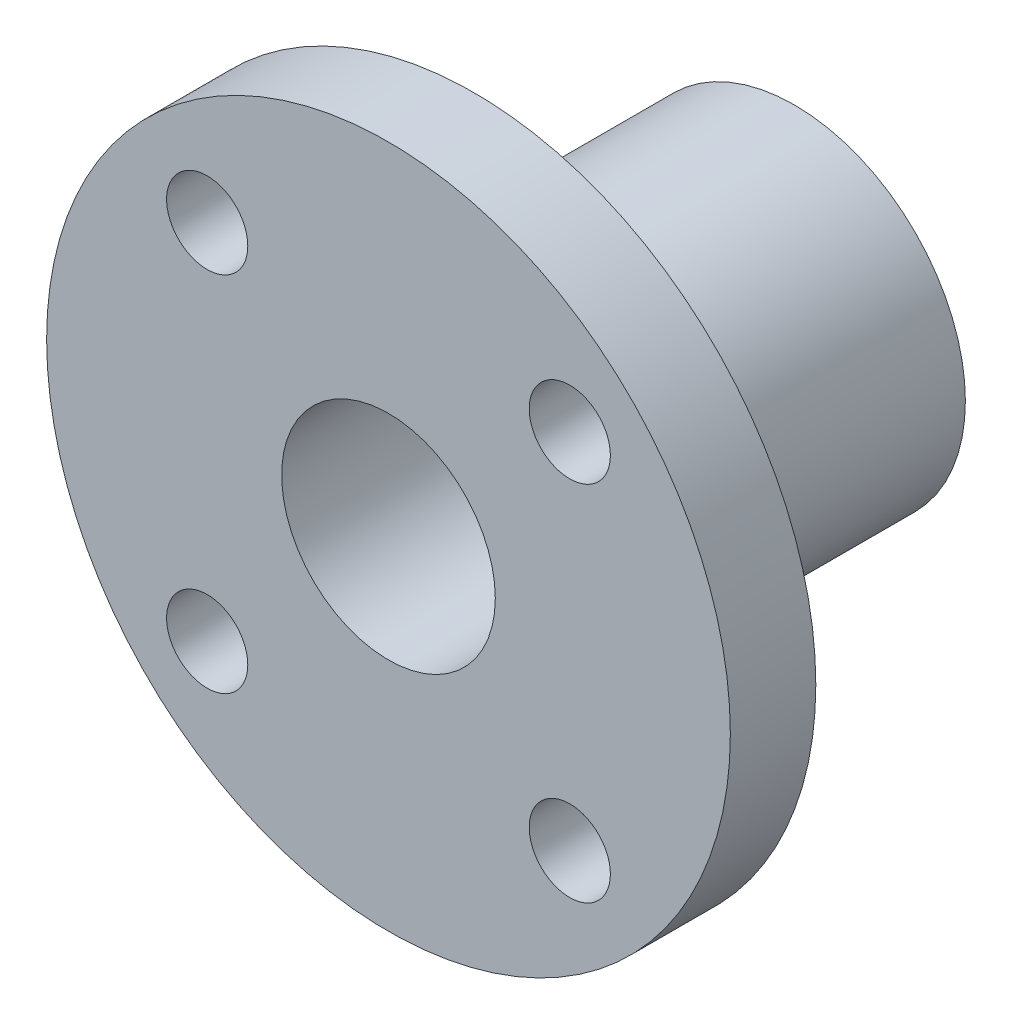
SolidWorks part; units mm, degrees
ref_plane "前视基准面" through (0, 0, 0) normal (0, 0, 1) x (1, 0, 0)
ref_plane "上视基准面" through (0, 0, 0) normal (0, 1, 0) x (1, 0, 0)
ref_plane "右视基准面" through (0, 0, 0) normal (1, 0, 0) x (0, 0, -1)
sketch "Sketch1" plane through (0, 0, 0) normal (0, 0, 1) x (1, 0, 0)
  circle A0 centre (0, 0) radius 8
  circle A1 centre (0, 0) radius 5
  dimension "D1" = 16
  dimension "D2" = 10
extrude "Extrude1" add sketch "Sketch1" along normal blind 15
sketch "Sketch2" plane through (0, 0, 15) normal (0, 0, 1) x (1, 0, 0)
  line L1 (-8.4853, -8.4853) -> (8.4853, -8.4853) construction
  line L2 (-8.4853, -8.4853) -> (-8.4853, 8.4853) construction
  line L3 (-8.4853, 8.4853) -> (8.4853, 8.4853) construction
  line L4 (8.4853, -8.4853) -> (8.4853, 8.4853) construction
  line L5 (-8.4853, -8.4853) -> (8.4853, 8.4853) construction
  line L6 (-8.4853, 8.4853) -> (8.4853, -8.4853) construction
  circle A0 centre (0, 0) radius 5
  circle A1 centre (0, 0) radius 16
  circle A2 centre (0, 0) radius 12 construction
  circle A3 centre (-8.4853, 8.4853) radius 1.9
  circle A4 centre (8.4853, 8.4853) radius 1.9
  circle A5 centre (-8.4853, -8.4853) radius 1.9
  circle A6 centre (8.4853, -8.4853) radius 1.9
  dimension "D1" = 32
  dimension "D2" = 24
  dimension "D3" = 3.8
extrude "Extrude2" add sketch "Sketch2" along normal blind 4
